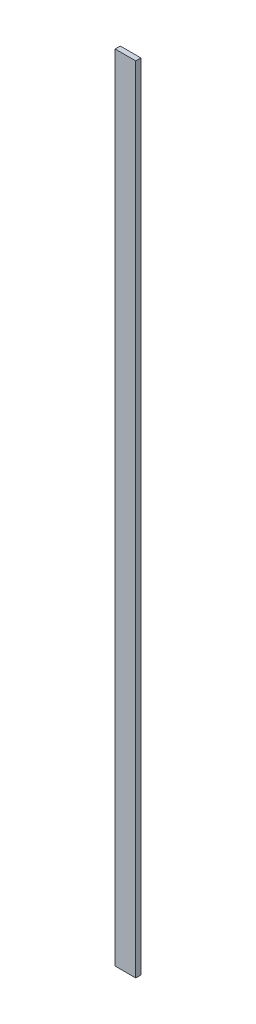
SolidWorks part; units mm, degrees
ref_plane "Plan de face" through (0, 0, 0) normal (0, 0, 1) x (1, 0, 0)
ref_plane "Plan de dessus" through (0, 0, 0) normal (0, 1, 0) x (1, 0, 0)
ref_plane "Plan de droite" through (0, 0, 0) normal (1, 0, 0) x (0, 0, -1)
sketch "Esquisse1" plane through (0, 0, 0) normal (0, 0, 1) x (1, 0, 0)
  line L1 (0, 0) -> (2, 0)
  line L2 (0, 0) -> (0, -77)
  line L3 (0, -77) -> (2, -77)
  line L4 (2, 0) -> (2, -77)
  dimension "D1" = 77
  dimension "D2" = 2
extrude "Boss.-Extru.1" add sketch "Esquisse1" along normal blind 0.5
